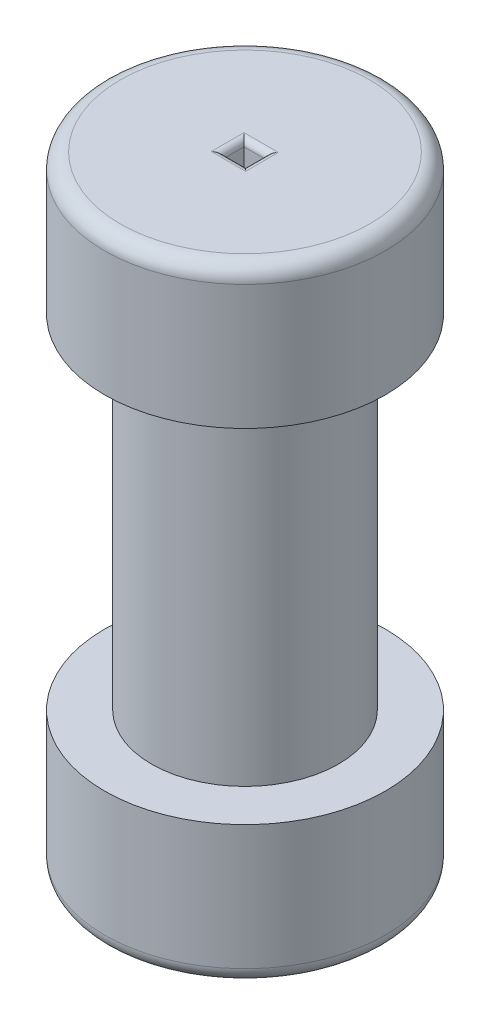
SolidWorks part; units mm, degrees
ref_plane "Front Plane" through (0, 0, 0) normal (0, 0, 1) x (1, 0, 0)
ref_plane "Top Plane" through (0, 0, 0) normal (0, 1, 0) x (1, 0, 0)
ref_plane "Right Plane" through (0, 0, 0) normal (1, 0, 0) x (0, 0, -1)
sketch "Sketch1" plane through (0, 0, 0) normal (0, 1, 0) x (1, 0, 0)
  circle A0 centre (0, 0) radius 22.86
  dimension "D1" = 45.72
extrude "Boss-Extrude1" add sketch "Sketch1" along normal blind 22.86
sketch "Sketch3" plane through (0, 22.86, 0) normal (0, 1, 0) x (1, 0, 0)
  circle A0 centre (0, 0) radius 15.24
  dimension "D1" = 30.48
extrude "Boss-Extrude2" add sketch "Sketch3" along normal blind 55.88
sketch "Sketch4" plane through (0, 78.74, 0) normal (0, 1, 0) x (1, 0, 0)
  circle A0 centre (0, 0) radius 22.86
  dimension "D1" = 45.72
extrude "Boss-Extrude3" add sketch "Sketch4" along normal blind 22.86
fillet "Fillet3" radius 2.54 2 edges at (0, 0, 22.86) (0, 101.6, 22.86)
sketch "Sketch5" plane through (0, 101.6, 0) normal (0, 1, 0) x (1, 0, 0)
  line L0 (-1.8, -0.03) -> (-1.8, -1.7)
  line L1 (-1.8, -1.7) -> (1.8, -1.7)
  line L2 (1.8, -1.7) -> (1.8, 1.64)
  line L3 (1.8, 1.64) -> (-1.8, 1.64)
  line L4 (-1.8, 1.64) -> (-1.8, -0.03)
  point P0 (0, 0)
  dimension "D1" = 3.6
  dimension "D2" = 1.7
  dimension "D3" = 1.8
extrude "Cut-Extrude1" cut sketch "Sketch5" against normal through all
fillet "Fillet4" radius 1 8 edges at (0, 101.6, 1.7) (1.8, 101.6, 0.03) (-1.8, 101.6, 0.03) (0, 101.6, -1.64) (0, 0, 1.7) (-1.8, 0, 0.03) (1.8, 0, 0.03) (0, 0, -1.64)
